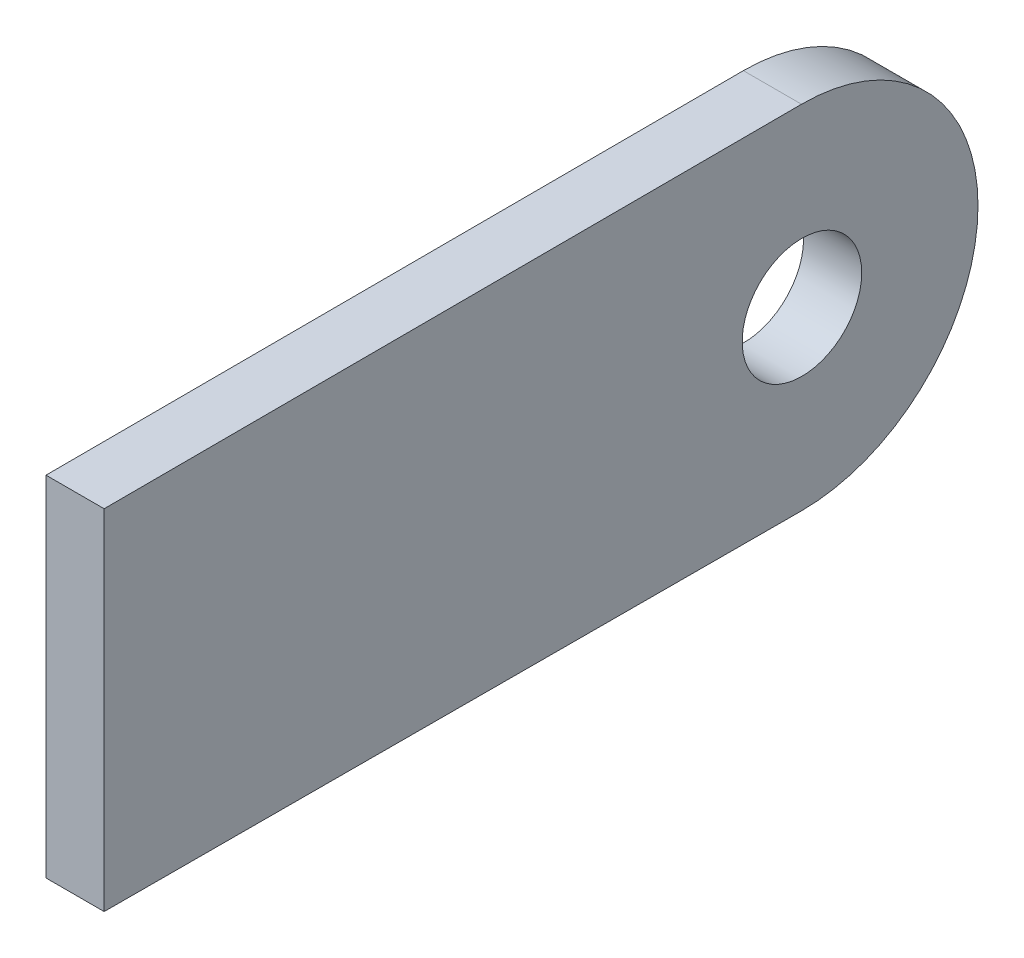
SolidWorks part; units mm, degrees
material "AISI 4130 Steel, annealed at 865C"
ref_plane "X-Y Datum" through (0, 0, 0) normal (0, 0, 1) x (1, 0, 0)
ref_plane "X-Z Datum" through (0, 0, 0) normal (0, 1, 0) x (1, 0, 0)
ref_plane "Y-Z Datum" through (0, 0, 0) normal (1, 0, 0) x (0, 0, -1)
sketch "Sketch1" plane through (0, 0, 0) normal (1, 0, 0) x (0, 0, -1)
  line L0 (0, 0) -> (-38.1, 0) construction
  line L1 (-38.1, 9.525) -> (-38.1, -9.525)
  line L2 (-0.0224, 9.6139) -> (-38.1, 9.525)
  line L3 (-0.0224, -9.6139) -> (-38.1, -9.525)
  circle A0 centre (0, 0) radius 3.2639
  arc A1 (-0.0224, -9.6139) -> (-0.0224, 9.6139) centre (0, 0) ccw
  point P7 (-38.1, 0)
  dimension "D1" = 6.5278
  dimension "D2" = 6.35
  dimension "D4" = 19.05
extrude "Boss-Extrude1" add sketch "Sketch1" along normal mid plane 3.175
